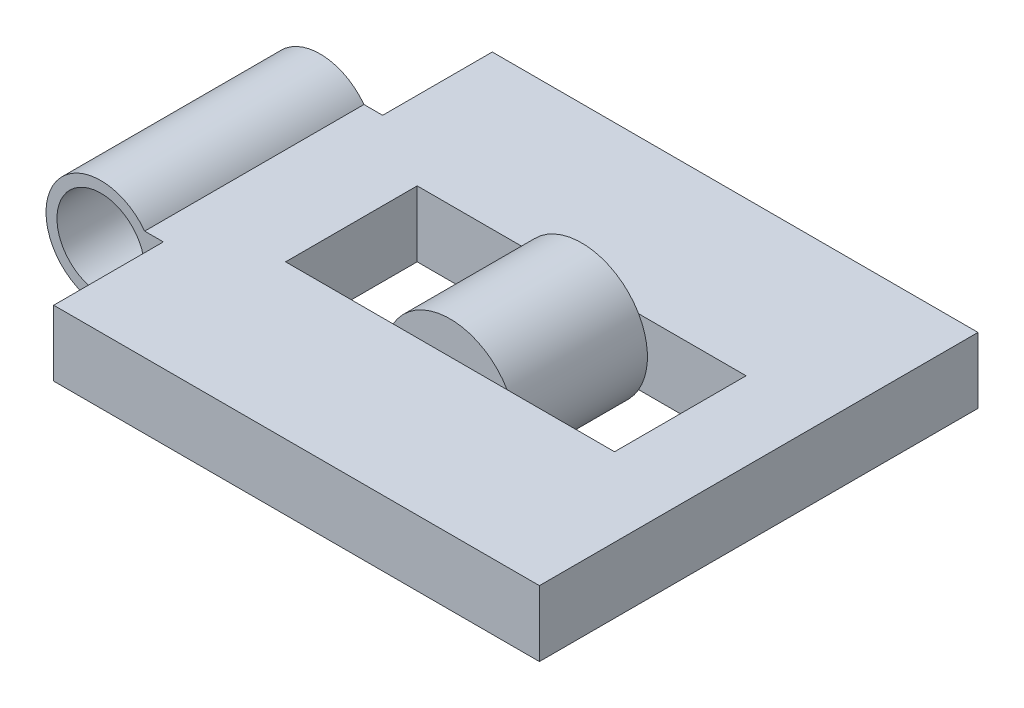
SolidWorks part; units mm, degrees
ref_plane "Front Plane" through (0, 0, 0) normal (0, 0, 1) x (1, 0, 0)
ref_plane "Top Plane" through (0, 0, 0) normal (0, 1, 0) x (1, 0, 0)
ref_plane "Right Plane" through (0, 0, 0) normal (1, 0, 0) x (0, 0, -1)
sketch "Sketch1" plane through (0, 0, 0) normal (0, 0, 1) x (1, 0, 0)
  line L1 (127, -7.62) -> (10.16, -7.62)
  line L2 (127, -7.62) -> (127, 7.62)
  line L3 (127, 7.62) -> (10.16, 7.62)
  line L4 (10.16, -7.62) -> (10.16, 7.62)
  line L5 (127, -7.62) -> (10.16, 7.62) construction
  line L6 (127, 7.62) -> (10.16, -7.62) construction
  circle A0 centre (0, 0) radius 12.7
  circle A1 centre (0, 0) radius 10.16
  point P6 (68.58, 0)
  dimension "D1" = 2.54
  dimension "D2" = 25.4
  dimension "D3" = 15.24
  dimension "D4" = 127
extrude "Boss-Extrude1" add sketch "Sketch1" along normal blind 101.6 contours A0 L1 L2 L3 | L4 A1 A0 | L4 A0
sketch "Sketch2" plane through (0, 7.62, 0) normal (0, 1, 0) x (1, 0, 0)
  line L1 (-12.7, -101.6) -> (14.4847, -101.6)
  line L2 (-12.7, -101.6) -> (-12.7, -76.2)
  line L3 (-12.7, -76.2) -> (14.4847, -76.2)
  line L4 (14.4847, -101.6) -> (14.4847, -76.2)
  line L6 (-12.7, 0) -> (14.4847, 0)
  line L7 (-12.7, 0) -> (-12.7, -25.4)
  line L8 (-12.7, -25.4) -> (14.4847, -25.4)
  line L9 (14.4847, 0) -> (14.4847, -25.4)
  dimension "D1" = 50.8
  dimension "D2" = 27.1847
extrude "Cut-Extrude1" cut sketch "Sketch2" against normal through all both and the other way through all contours L7 L6 L9 L8 | L2 L1 L4 L3
sketch "Sketch3" plane through (0, -7.62, 0) normal (0, -1, 0) x (1, 0, 0)
  line L0 (127, 0) -> (14.4847, 0) construction
  line L1 (108.8424, 35.56) -> (32.6424, 35.56)
  line L2 (108.8424, 35.56) -> (108.8424, 66.04)
  line L3 (108.8424, 66.04) -> (32.6424, 66.04)
  line L4 (32.6424, 35.56) -> (32.6424, 66.04)
  line L5 (108.8424, 35.56) -> (32.6424, 66.04) construction
  line L6 (108.8424, 66.04) -> (32.6424, 35.56) construction
  line L7 (127, 101.6) -> (127, 0) construction
  point P0 (70.7424, 50.8)
  point P5 (0, 0)
  point P8 (70.7424, 0)
  point P9 (70.7424, 50.7032)
  point P12 (127, 50.8)
  dimension "D1" = 76.2
  dimension "D2" = 30.48
extrude "Cut-Extrude2" cut sketch "Sketch3" against normal through all
sketch "Sketch4" plane through (0, 0, 35.56) normal (0, 0, 1) x (1, 0, 0)
  circle A0 centre (70.7424, 0) radius 15.24
  point P2 (0, 0)
  point P4 (0, 0)
  dimension "D1" = 30.48
extrude "Boss-Extrude2" add sketch "Sketch4" along normal up to surface (30.48 mm away) up to face at (70.7424, 0, 66.04)
